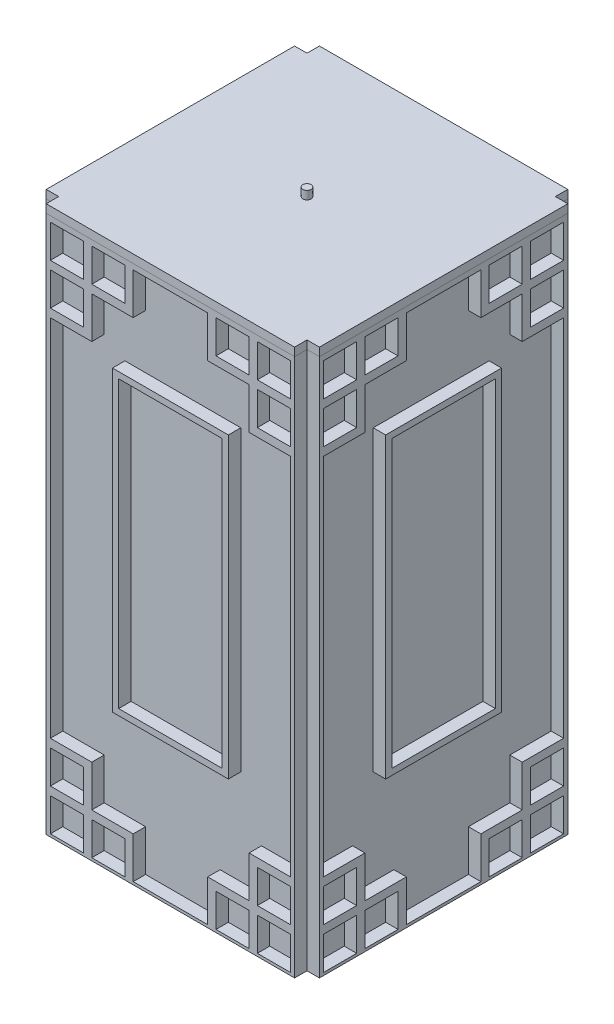
SolidWorks part; units mm, degrees
ref_plane "前视基准面" through (0, 0, 0) normal (0, 0, 1) x (1, 0, 0)
ref_plane "上视基准面" through (0, 0, 0) normal (0, 1, 0) x (1, 0, 0)
ref_plane "右视基准面" through (0, 0, 0) normal (1, 0, 0) x (0, 0, -1)
sketch "草图1" plane through (0, 0, 0) normal (0, 1, 0) x (1, 0, 0)
  line L1 (-150, 150) -> (150, 150)
  line L2 (-150, 150) -> (-150, -150)
  line L3 (-150, -150) -> (150, -150)
  line L4 (150, 150) -> (150, -150)
  line L5 (-150, 150) -> (150, -150) construction
  line L6 (-150, -150) -> (150, 150) construction
  point P0 (0, 0)
extrude "凸台-拉伸1" add sketch "草图1" along normal blind 650
shell "抽壳1" thickness 10
ref_plane "灯面1" through (0, 0, 150) normal (0, 0, 1) x (1, 0, 0)
sketch "草图6" plane through (0, 0, 150) normal (0, 0, 1) x (1, 0, 0)
  line L0 (-150, 650) -> (-150, 0)
  line L1 (-150, 0) -> (150, 0)
  line L2 (150, 0) -> (150, 650)
  line L3 (150, 650) -> (-150, 650)
  line L4 (0, 755.1624) -> (0, -108.5632) construction
  line L5 (-95, 643.2996) -> (-95, 603.2996)
  line L6 (-145, 643.2996) -> (-105, 643.2996)
  line L7 (-145, 643.2996) -> (-145, 603.2996)
  line L8 (-95, 3.2996) -> (-55, 3.2996)
  line L9 (145, 643.2996) -> (145, 603.2996)
  line L10 (-105, 593.2996) -> (-105, 553.2996)
  line L11 (-101.1732, 543.2996) -> (-145, 543.2996)
  line L12 (-95, 543.2996) -> (-145, 543.2996)
  line L13 (-45, 643.2996) -> (-45, 593.2996)
  line L14 (-45, 593.2996) -> (-95, 593.2996)
  line L15 (-105, 643.2996) -> (-105, 603.2996)
  line L16 (-95, 593.2996) -> (-95, 543.2996)
  line L17 (-95, 603.2996) -> (-55, 603.2996)
  line L18 (-145, 603.2996) -> (-105, 603.2996)
  line L19 (-55, 643.2996) -> (-55, 603.2996)
  line L20 (-145, 553.2996) -> (-105, 553.2996)
  line L21 (-105, 593.2996) -> (-145, 593.2996)
  line L22 (-145, 593.2996) -> (-145, 553.2996)
  line L23 (-95, 643.2996) -> (-55, 643.2996)
  line L24 (-45, 643.2996) -> (45, 643.2996)
  line L25 (-145, 543.2996) -> (-145, 103.2996)
  line L26 (-214.6527, 323.2996) -> (225.0166, 323.2996) construction
  line L27 (95, 543.2996) -> (145, 543.2996)
  line L28 (45, 643.2996) -> (45, 593.2996)
  line L29 (45, 593.2996) -> (95, 593.2996)
  line L30 (95, 593.2996) -> (95, 543.2996)
  line L31 (95, 603.2996) -> (55, 603.2996)
  line L32 (55, 643.2996) -> (55, 603.2996)
  line L33 (95, 643.2996) -> (55, 643.2996)
  line L34 (95, 643.2996) -> (95, 603.2996)
  line L35 (145, 603.2996) -> (105, 603.2996)
  line L36 (145, 643.2996) -> (145, 603.2996)
  line L37 (105, 643.2996) -> (105, 603.2996)
  line L38 (145, 643.2996) -> (105, 643.2996)
  line L39 (145, 553.2996) -> (105, 553.2996)
  line L40 (145, 593.2996) -> (145, 553.2996)
  line L41 (105, 593.2996) -> (145, 593.2996)
  line L42 (105, 593.2996) -> (105, 553.2996)
  line L43 (55, 643.2996) -> (95, 643.2996)
  line L44 (105, 643.2996) -> (145, 643.2996)
  line L45 (145, 593.2996) -> (145, 553.2996)
  line L46 (145, 543.2996) -> (145, 103.2996)
  line L47 (95, 103.2996) -> (145, 103.2996)
  line L48 (45, 3.2996) -> (45, 53.2996)
  line L49 (45, 53.2996) -> (95, 53.2996)
  line L50 (95, 53.2996) -> (95, 103.2996)
  line L51 (145, 53.2996) -> (145, 93.2996)
  line L52 (105, 53.2996) -> (145, 53.2996)
  line L53 (105, 53.2996) -> (105, 93.2996)
  line L54 (145, 93.2996) -> (105, 93.2996)
  line L55 (145, 3.2996) -> (105, 3.2996)
  line L56 (105, 3.2996) -> (105, 43.2996)
  line L57 (145, 43.2996) -> (105, 43.2996)
  line L58 (145, 3.2996) -> (145, 43.2996)
  line L59 (95, 43.2996) -> (55, 43.2996)
  line L60 (95, 3.2996) -> (95, 43.2996)
  line L61 (95, 3.2996) -> (55, 3.2996)
  line L62 (55, 3.2996) -> (55, 43.2996)
  line L63 (-45, 3.2996) -> (-45, 53.2996)
  line L64 (-45, 53.2996) -> (-95, 53.2996)
  line L65 (-95, 53.2996) -> (-95, 103.2996)
  line L66 (-95, 103.2996) -> (-145, 103.2996)
  line L67 (-105, 53.2996) -> (-105, 93.2996)
  line L68 (-145, 93.2996) -> (-105, 93.2996)
  line L69 (-145, 53.2996) -> (-145, 93.2996)
  line L70 (-105, 53.2996) -> (-145, 53.2996)
  line L71 (-95, 43.2996) -> (-55, 43.2996)
  line L72 (-55, 3.2996) -> (-55, 43.2996)
  line L73 (-95, 3.2996) -> (-95, 43.2996)
  line L74 (-145, 43.2996) -> (-105, 43.2996)
  line L75 (-105, 3.2996) -> (-105, 43.2996)
  line L76 (-145, 3.2996) -> (-145, 43.2996)
  line L77 (-95, 3.2996) -> (-55, 3.2996)
  line L78 (-145, 3.2996) -> (-105, 3.2996)
  line L79 (-145, 93.2996) -> (-145, 53.2996)
  line L80 (-145, 43.2996) -> (-145, 3.2996)
  line L81 (-45, 3.2996) -> (45, 3.2996)
  line L82 (145, 93.2996) -> (145, 53.2996)
  line L83 (145, 43.2996) -> (145, 3.2996)
  line L84 (55, 3.2996) -> (95, 3.2996)
  line L85 (105, 3.2996) -> (145, 3.2996)
  point P11 (0, 323.2996)
extrude "凸台-拉伸2" add sketch "草图6" along normal blind 15 contours L2 L3 L0 L1 L81 L63 L64 L65 L66 L25 L11 L12 L16 L14 L13 L24 L28 L29 L30 L27 L46 L47 L50 L49 L48 L78 L76 L74 L75 L58 L55 L56 L57 L54 L51 L52 L53 L42 L41 L40 L39 L38 L9 L35 L37
sketch "草图7" plane through (0, 0, 150) normal (0, 0, 1) x (1, 0, 0)
  line L0 (0, 731.882) -> (0, -35.6525) construction
  line L2 (-62.5, 520.6148) -> (62.5, 520.6148)
  line L3 (-62.5, 520.6148) -> (-62.5, 175.6148)
  line L4 (-62.5, 175.6148) -> (62.5, 175.6148)
  line L5 (62.5, 520.6148) -> (62.5, 175.6148)
  line L6 (-70, 528.1148) -> (70, 528.1148)
  line L7 (-70, 528.1148) -> (-70, 168.1148)
  line L8 (-70, 168.1148) -> (70, 168.1148)
  line L9 (70, 528.1148) -> (70, 168.1148)
  point P3 (0, 348.1148)
  point P8 (0, 348.1148)
extrude "凸台-拉伸3" add sketch "草图7" along normal blind 15 contours L7 L6 L9 L8 | L3 L2 L5 L4
sketch "草图9" plane through (0, 0, 0) normal (0, 1, 0) x (1, 0, 0)
  line L0 (0, 158.6102) -> (0, -180.5768) construction
  line L1 (173.2945, 0) -> (-182.0028, 0) construction
ref_plane "基准面2" through (0, 0, 0) normal (0, 0, -1) x (-1, 0, 0)
mirror "镜向1" about plane through (0, 0, 0) normal (0, 0, -1) of "凸台-拉伸2", "凸台-拉伸3"
sketch "草图12" plane through (0, 0, 0) normal (0, 1, 0) x (1, 0, 0)
  line L0 (140, -140) -> (-140, 140) construction
ref_plane "基准面4" through (0, 0, 0) normal (-0.7071, 0, 0.7071) x (0.7071, 0, 0.7071)
mirror "镜向3" about plane through (0, 0, 0) normal (-0.7071, 0, 0.7071) of "凸台-拉伸2", "凸台-拉伸3"
ref_plane "基准面6" through (0, 0, 0) normal (-1, 0, 0) x (0, 0, 1)
mirror "镜向5" about plane through (0, 0, 0) normal (-1, 0, 0) of "镜向3"
ref_plane "基准面7" through (0, 660, 0) normal (0, 1, 0) x (1, 0, 0)
sketch "草图14" plane through (0, 660, 0) normal (0, 1, 0) x (1, 0, 0)
  line L0 (-150, 165) -> (-150, 150)
  line L1 (-150, 150) -> (-165, 150)
  line L2 (-165, 150) -> (-165, -150)
  line L3 (-165, -150) -> (-150, -150)
  line L4 (-150, -150) -> (-150, -165)
  line L5 (-150, -165) -> (150, -165)
  line L6 (150, -165) -> (150, -150)
  line L7 (150, -150) -> (165, -150)
  line L8 (165, -150) -> (165, 150)
  line L9 (165, 150) -> (150, 150)
  line L10 (150, 150) -> (150, 165)
  line L11 (150, 165) -> (-150, 165)
extrude "凸台-拉伸4" add sketch "草图14" against normal blind 10 separate body
sketch "草图15" plane through (0, 660, 0) normal (0, 1, 0) x (1, 0, 0)
  circle A0 centre (0, 0) radius 5
extrude "凸台-拉伸5" add sketch "草图15" along normal blind 10 contours A0
